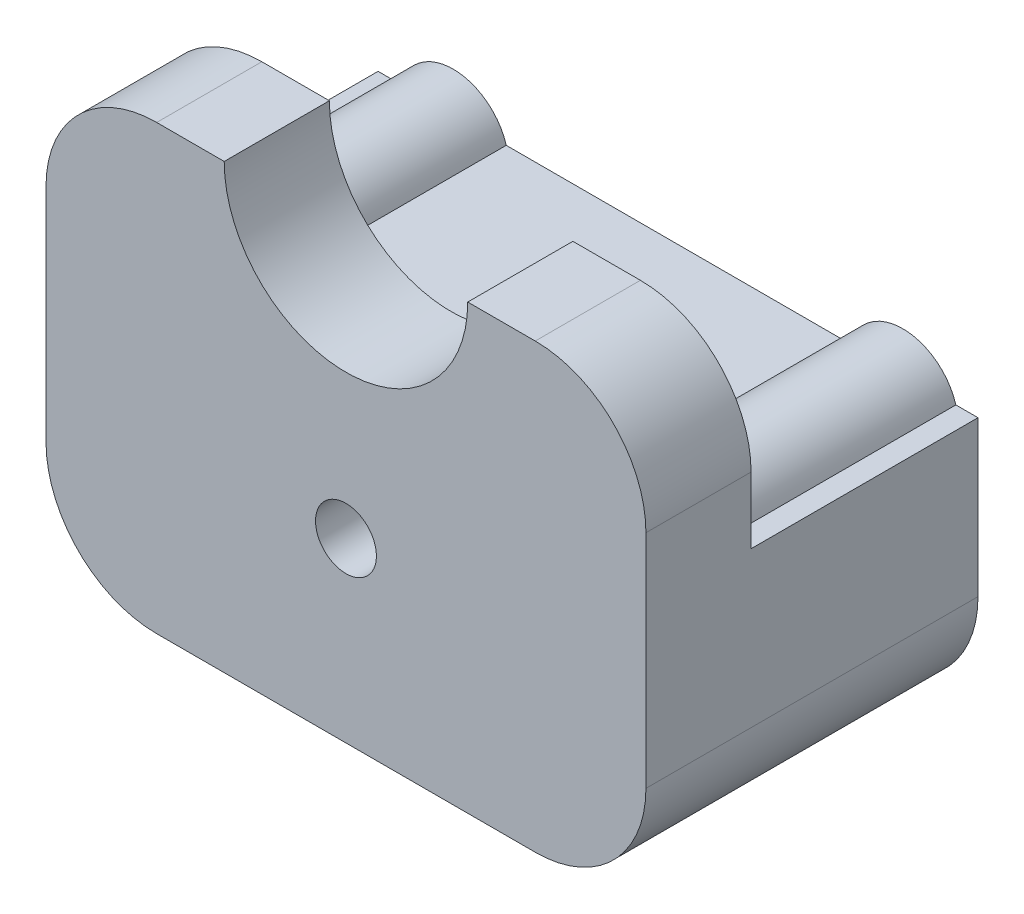
SolidWorks part; units mm, degrees
ref_plane "Front Plane" through (0, 0, 0) normal (0, 0, 1) x (1, 0, 0)
ref_plane "Top Plane" through (0, 0, 0) normal (0, 1, 0) x (1, 0, 0)
ref_plane "Right Plane" through (0, 0, 0) normal (1, 0, 0) x (0, 0, -1)
sketch "Sketch1" plane through (0, 0, 0) normal (0, 0, 1) x (1, 0, 0)
  line L0 (-49.5167, 22.8098) -> (-46.2, 4)
  line L1 (0, 0) -> (-54.2, 0)
  line L2 (-54.2, 25) -> (-54.2, 40)
  line L3 (0, 25) -> (-54.2, 25)
  line L4 (-54.2, 0) -> (-54.2, 25)
  line L5 (-46.2, 4) -> (-8, 4)
  line L6 (0, 25) -> (0, 0)
  line L7 (-8, 4) -> (-4.6833, 22.8098)
  line L8 (-4.6833, 22.8098) -> (-8.6226, 23.5044)
  line L9 (-8.6226, 23.5044) -> (-11.3564, 8)
  line L10 (-11.3564, 8) -> (-42.8436, 8)
  line L11 (-42.8436, 8) -> (-45.5774, 23.5044)
  line L12 (-45.5774, 23.5044) -> (-49.5167, 22.8098)
  line L13 (-38.1, 40) -> (-54.2, 40)
  line L14 (0, 25) -> (0, 40)
  line L15 (-16.1, 40) -> (0, 40)
  arc A0 (-38.1, 40) -> (-16.1, 40) centre (-27.1, 40) ccw
  dimension "D15" = 15
  dimension "D17" = 0
  dimension "D14" = 11
  dimension "D1" = 25
  dimension "D2" = 8
  dimension "D3" = 4
  dimension "D4" = 4
  dimension "D5" = 4
  dimension "D6" = 19.1
  dimension "D7" = 19.1
  dimension "D8" = 38.2
  dimension "D9" = 100
  dimension "D10" = 100
  dimension "D11" = 8
  dimension "D12" = 4
  dimension "D13" = 1.4956
  dimension "D16" = 15
  dimension "D18" = 16.1
  dimension "D19" = 16.1
extrude "Boss-Extrude1" add sketch "Sketch1" along normal blind 25 contours L6 L3 L4 L1 L12 L11 L10 L9 L8 L7 L5 L0 | A0 L13 L2 L3 | A0 L3 L14 L15
sketch "Sketch2" plane through (0, 0, 25) normal (0, 0, 1) x (1, 0, 0)
  line L0 (-54.2, 40) -> (-54.2, 0)
  line L1 (-54.2, 0) -> (0, 0)
  line L2 (0, 0) -> (0, 40)
  line L3 (0, 40) -> (-16.1, 40)
  line L4 (-54.2, 40) -> (-38.1, 40)
  arc A0 (-38.1, 40) -> (-16.1, 40) centre (-27.1, 40) ccw
  dimension "D1" = 11
extrude "Boss-Extrude2" add sketch "Sketch2" along normal blind 5
sketch "Sketch4" plane through (0, 0, 0) normal (0, 0, -1) x (-1, 0, 0)
  line L0 (16.1, 40) -> (0, 40)
  line L1 (0, 40) -> (0, 24)
  line L2 (0, 40) -> (0, 0) construction
  line L3 (0, 24) -> (2, 24)
  line L4 (54.2, 0) -> (54.2, 40) construction
  line L5 (54.2, 24) -> (54.2, 40)
  line L6 (54.2, 40) -> (38.1, 40)
  line L7 (38.1, 40) -> (54.2, 40) construction
  line L8 (11.5813, 24) -> (42.6187, 24)
  line L9 (54.2, 24) -> (52.2, 24)
  line L10 (0, 24) -> (0, 40)
  line L11 (0, 40) -> (16.1, 40)
  arc A0 (16.1, 40) -> (38.1, 40) centre (27.1, 40) ccw construction
  arc A1 (2, 24) -> (11.5813, 24) centre (6.7907, 22.5684) cw
  arc A2 (42.6187, 24) -> (52.2, 24) centre (47.4093, 22.5684) cw
  arc A3 (16.1, 40) -> (38.1, 40) centre (27.1, 40) ccw
  line M14 (0, 40) -> (0, 0)
  line M16 (54.2, 0) -> (54.2, 40)
  line M17 (54.2, 40) -> (38.1, 40)
  arc M18 (38.1, 40) -> (16.1, 40) centre (27.1, 40) cw
  line M19 (16.1, 40) -> (0, 40)
  dimension "D8" = 16.1
  dimension "D12" = 5
  dimension "D13" = 5
  dimension "D16" = 11
  dimension "D1" = 2
  dimension "D2" = 16
  dimension "D3" = 2.9354
  dimension "D4" = 3
  dimension "D5" = 3
  dimension "D6" = 16.1
  dimension "D7" = 2
  dimension "D9" = 31.0373
  dimension "D10" = 9.5813
  dimension "D11" = 9.5813
  dimension "D14" = 2.9354
  dimension "D15" = 16
fillet "Fillet1" radius 10 2 edges at (0, 0, 15) (-54.2, 0, 15)
fillet "Fillet2" radius 10 2 edges at (0, 40, 15) (-54.2, 40, 15)
extrude "Cut-Extrude1" cut sketch "Sketch4" against normal blind 20.5 contours L8 A2 L9 L3 A1 M16 M17 M18 M19 M14
sketch "Sketch5" plane through (0, 0, 0) normal (0, 0, -1) x (-1, 0, 0)
  line L0 (11.5813, 24) -> (42.6187, 24) construction
  line L1 (11.3564, 8) -> (42.8436, 8) construction
  line L2 (54.2, 10) -> (54.2, 24) construction
  line L3 (0, 24) -> (0, 10) construction
  circle A0 centre (27.1, 16) radius 2.75
  point P6 (27.1, 8)
  dimension "D1" = 5.5
  dimension "D2" = 8
  dimension "D3" = 8
  dimension "D4" = 27.1
  dimension "D5" = 27.1
extrude "Cut-Extrude2" cut sketch "Sketch5" against normal blind 30
